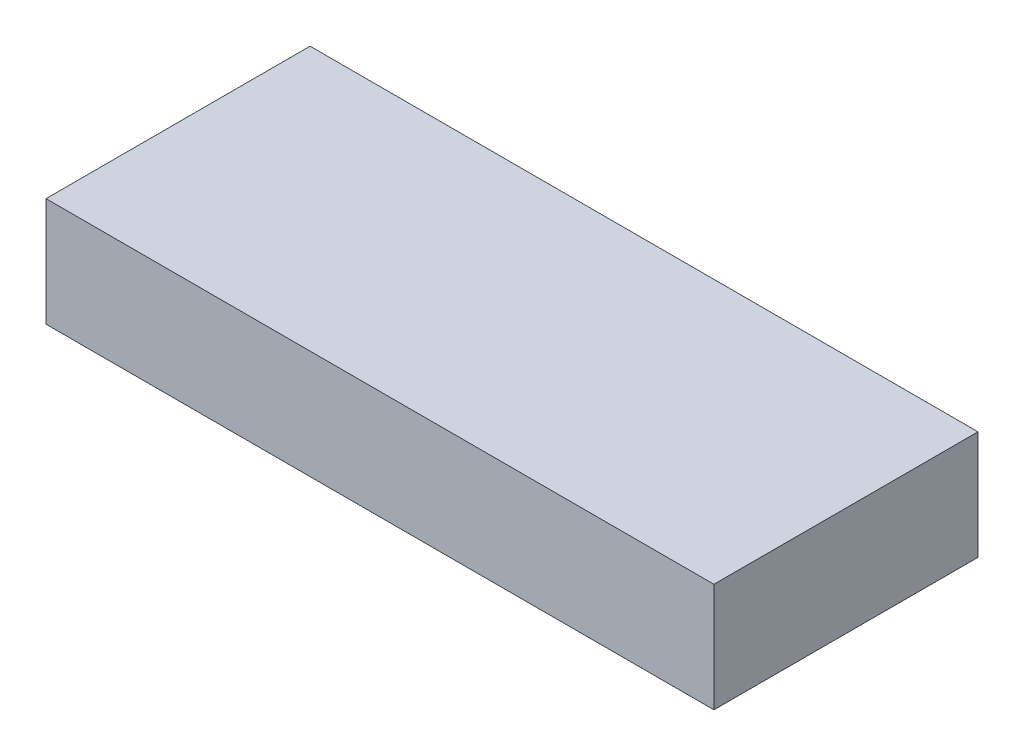
SolidWorks part; units mm, degrees
ref_plane "Front Plane" through (0, 0, 0) normal (0, 0, 1) x (1, 0, 0)
ref_plane "Top Plane" through (0, 0, 0) normal (0, 1, 0) x (1, 0, 0)
ref_plane "Right Plane" through (0, 0, 0) normal (1, 0, 0) x (0, 0, -1)
sketch "Sketch1" plane through (0, 0, 0) normal (0, 1, 0) x (1, 0, 0)
  line L1 (0, 0) -> (43, 0)
  line L2 (0, 0) -> (0, 17)
  line L3 (0, 17) -> (43, 17)
  line L4 (43, 0) -> (43, 17)
  dimension "D1" = 17
  dimension "D2" = 43
extrude "Boss-Extrude1" add sketch "Sketch1" along normal blind 7
